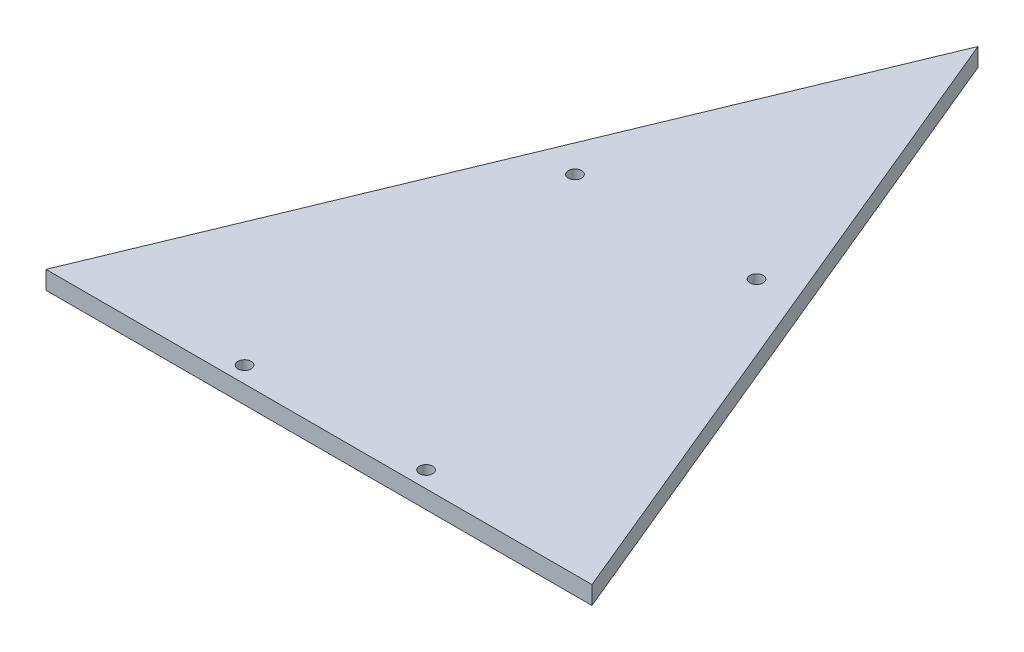
SolidWorks part; units mm, degrees
material "6061-T6 (SS)"
ref_plane "Front Plane" through (0, 0, 0) normal (0, 0, 1) x (1, 0, 0)
ref_plane "Top Plane" through (0, 0, 0) normal (0, 1, 0) x (1, 0, 0)
ref_plane "Right Plane" through (0, 0, 0) normal (1, 0, 0) x (0, 0, -1)
sketch "Sketch1" plane through (0, 0, 0) normal (0, 1, 0) x (1, 0, 0)
  line L1 (75.1798, 0) -> (0, 181.5)
  line L3 (75.1798, 0) -> (-75.1798, 0)
  line L4 (-75.1798, 0) -> (0, 181.5)
  line L5 (0, 0) -> (0, 181.5)
  line L6 (27.7018, 4.3789) -> (0, 4.3789)
  line L7 (0, 4.3789) -> (-27.7018, 4.3789)
  line L10 (0, 0) -> (0, 100.1636)
  circle A2 centre (27.7018, 4.3789) radius 2
  circle A3 centre (-27.7018, 4.3789) radius 2
  circle A4 centre (-27.7018, 95.6211) radius 2
  circle A5 centre (27.7018, 95.6211) radius 2
  point P0 (0, 0)
  dimension "D3" = 4.3789
  dimension "D1" = 45
  dimension "D2" = 181.5
  dimension "D4" = 55.4037
  dimension "D5" = 91.2422
extrude "Boss-Extrude1" add sketch "Sketch1" along normal blind 5
sketch "Sketch2" plane through (0, 5, 0) normal (0, 1, 0) x (1, 0, 0)
  line L0 (75.1798, 0) -> (0, 181.5)
  line L1 (0, 181.5) -> (-75.1798, 0)
  line L2 (-75.1798, 0) -> (75.1798, 0)
  line L3 (0, 0) -> (0, 25.2143)
  circle A0 centre (27.7018, 4.3789) radius 2
  circle A1 centre (-27.7018, 4.3789) radius 2
  circle A2 centre (-27.7018, 95.6211) radius 2
  circle A3 centre (27.7018, 95.6211) radius 2
sketch "Sketch3" plane through (0, 5, 0) normal (0, 1, 0) x (1, 0, 0)
  line L1 (-32.4759, 99.4424) -> (31.6906, 99.4424)
  line L2 (-32.4759, 99.4424) -> (-32.4759, 2.0043)
  line L3 (-32.4759, 2.0043) -> (31.6906, 2.0043)
  line L4 (31.6906, 99.4424) -> (31.6906, 2.0043)
extrude "Boss-Extrude2" add sketch "Sketch3" against normal up to surface (5 mm away) up to face at (-27.7018, 0, -2.3789)
sketch "Sketch4" plane through (0, 5, 0) normal (0, 1, 0) x (1, 0, 0)
  circle A0 centre (-25, 4.5) radius 1.825
  circle A1 centre (25, 4.5) radius 1.825
  circle A2 centre (25, 95.5) radius 1.825
  circle A3 centre (-25, 95.5) radius 1.825
  point P0 (0, 0)
  point P11 (-25, 4.5)
  point P12 (25, 4.5)
  point P13 (25, 95.5)
  point P14 (-25, 95.5)
  point P19 (0, 0)
extrude "Cut-Extrude1" cut sketch "Sketch4" against normal blind 10 contours A1 | A0 | A2 | A3
